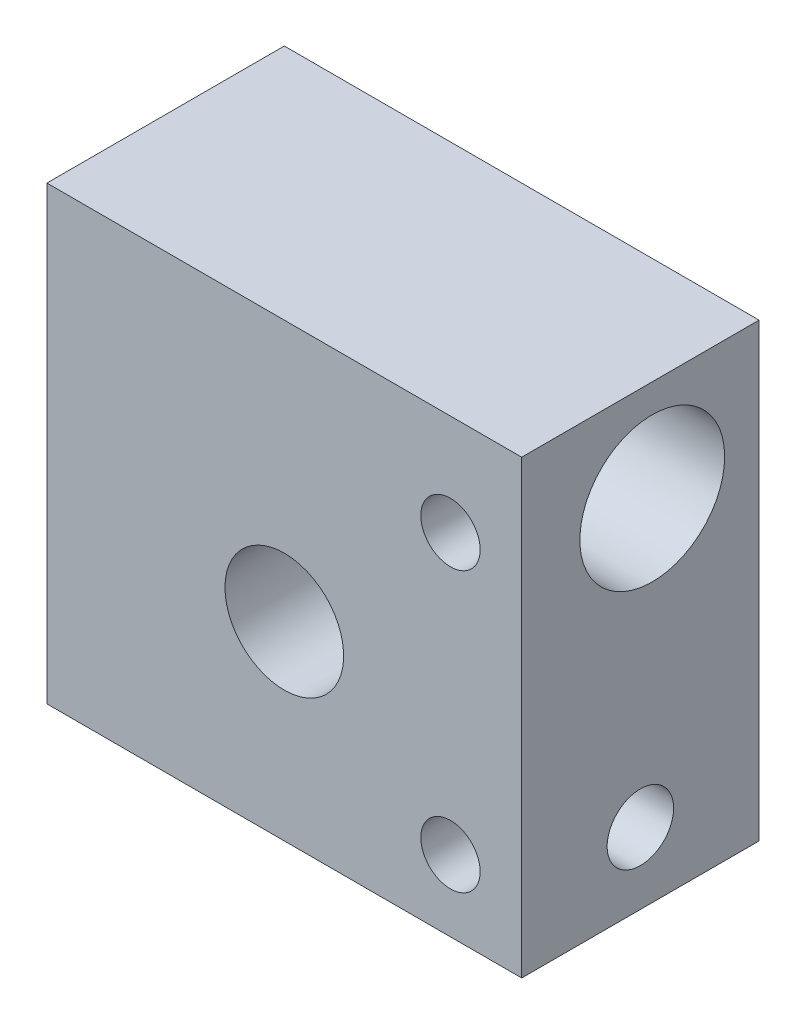
SolidWorks part; units mm, degrees
ref_plane "Front Plane" through (0, 0, 0) normal (0, 0, 1) x (1, 0, 0)
ref_plane "Top Plane" through (0, 0, 0) normal (0, 1, 0) x (1, 0, 0)
ref_plane "Right Plane" through (0, 0, 0) normal (1, 0, 0) x (0, 0, -1)
sketch "Sketch1" plane through (0, 0, 0) normal (0, 0, 1) x (1, 0, 0)
  line L1 (-10, -9.5) -> (10, -9.5)
  line L2 (-10, -9.5) -> (-10, 9.5)
  line L3 (-10, 9.5) -> (10, 9.5)
  line L4 (10, -9.5) -> (10, 9.5)
  line L5 (-10, -9.5) -> (10, 9.5) construction
  line L6 (-10, 9.5) -> (10, -9.5) construction
  point P0 (0, 0)
  dimension "D1" = 19
  dimension "D2" = 20
extrude "Boss-Extrude1" add sketch "Sketch1" along normal blind 10
sketch "Sketch2" plane through (0, 0, 0) normal (0, 0, -1) x (-1, 0, 0)
  line L0 (0, 9.5) -> (0, -9.5) construction
  line L1 (10, -9.5) -> (-10, -9.5) construction
  line L2 (-10, 9.5) -> (10, 9.5) construction
  circle A0 centre (0, -1.5) radius 2.5
  dimension "D1" = 5
  dimension "D2" = 8
extrude "Cut-Extrude1" cut sketch "Sketch2" against normal through all
cosmetic thread "Rosca cosmética1" parameters "D2"=6
sketch "Sketch3" plane through (10, 0, 0) normal (1, 0, 0) x (0, 0, -1)
  line L0 (-10, 0) -> (0, 0) construction
  line L1 (-10, -9.5) -> (-10, 9.5) construction
  line L2 (0, -9.5) -> (0, 9.5) construction
  line L3 (-4.5, 0) -> (-4.5, 9.5) construction
  line L5 (-10, 9.5) -> (0, 9.5) construction
  circle A0 centre (-4.5, 5.25) radius 3.05
  dimension "D1" = 6.1
  dimension "D3" = 4.5
  dimension "D2" = 1.2
extrude "Cut-Extrude2" cut sketch "Sketch3" against normal through all
sketch "Sketch4" plane through (10, 0, 0) normal (1, 0, 0) x (0, 0, -1)
  line L0 (0, -5) -> (-10, -5) construction
  line L3 (-5, -5) -> (-5, -9.5) construction
  line L4 (-10, -9.5) -> (0, -9.5) construction
  line L5 (0, -9.5) -> (0, 9.5) construction
  line L6 (-10, -9.5) -> (-10, 9.5) construction
  circle A0 centre (-5, -5) radius 1.4
  dimension "D1" = 2.8
  dimension "D2" = 4.5
extrude "Cut-Extrude3" [suppressed] cut sketch "Sketch4" against normal blind 4
hole_wizard "Diámetro de taladro Ø2.8 (2.8)1" positions "Croquis7" profile "Croquis6" hole size "Ø2.8" standard "Iso"
sketch "Croquis7" plane through (10, 0, 0) normal (1, 0, 0) x (0, 0, -1)
  line L0 (0, -6.5) -> (-10, -6.5) construction
  line L1 (0, -9.5) -> (0, 9.5) construction
  line L2 (-10, -9.5) -> (-10, 9.5) construction
  line L4 (-10, -9.5) -> (0, -9.5) construction
  point P0 (-5, -6.5)
  dimension "D1" = 3
sketch "Croquis6" plane through (10, -6.5, 5) normal (0, 1, 0) x (0, 0, -1)
  line L0 (0, 0) -> (0, 14.8412)
  line L1 (0, 14.8412) -> (1.4, 14)
  line L2 (1.4, 14) -> (1.4, 0)
  line L5 (1.4, 0) -> (0, 0)
  line L10 (0, 14.8412) -> (-1.4, 14) construction
  line L11 (0, -6.35) -> (0, 107.95) construction
  dimension "Diámetro de taladro" = 2.8
  dimension "Profundidad de taladro" = 14
  dimension "Ángulo de perforador" = 118
hole_wizard "Taladro roscado M31" positions "Croquis3" profile "Croquis2" tap size "M3" standard "Iso"
sketch "Croquis3" plane through (-2.6487, -2.9752, 10) normal (0, 0, -1) x (1, 0, 0)
  line L3 (12.6487, -8.2252) -> (-7.3513, -8.2252) construction
  line L4 (12.6487, 6.5248) -> (12.6487, -12.4752) construction
  line L5 (-7.3513, -12.4752) -> (-7.3513, 6.5248) construction
  line L7 (12.6487, -11.2752) -> (12.6487, -5.1752) construction
  line L8 (12.6487, 3.5248) -> (-7.3513, 3.5248) construction
  line L10 (12.6487, 2.1248) -> (12.6487, 4.9248) construction
  point P0 (9.6487, -8.2252)
  point P28 (9.6487, 3.5248)
  dimension "D1" = 3
  dimension "D2" = 3
sketch "Croquis2" plane through (7, 5.25, 10) normal (1, 0, 0) x (0, -1, 0)
  line L0 (0, 0) -> (0, 2.45)
  line L1 (0, 2.45) -> (1.25, 2.45)
  line L2 (1.25, 2.45) -> (1.25, 0)
  line L5 (1.25, 0) -> (0, 0)
  line L11 (0, -6.35) -> (0, 107.95) construction
  dimension "Diámetro de perforador para roscar hasta el siguiente" = 2.5
  dimension "Profundidad de perforador para roscar hasta el siguiente" = 2.45
cosmetic thread "Rosca de taladro1" parameters "D2"=3
cosmetic thread "Rosca de taladro4" parameters "D2"=3
sketch "Croquis4" [suppressed] plane through (0, 0, 0) normal (0, 0, -1) x (-1, 0, 0)
  line L2 (-9, -9) -> (-9, 9) construction
  line L3 (-9, -3.1) -> (-9, -5.9) construction
  line L4 (-9, -3.1) -> (-9, -5.9) construction
  line L5 (-9, -4.5) -> (-6.5, -4.5) construction
  line L6 (9, -9) -> (-9, -9) construction
  circle A0 centre (-6.5, -4.5) radius 1.5
  dimension "D1" = 1
  dimension "D2" = 3
extrude "Cortar-Extruir1" [suppressed] cut sketch "Croquis4" against normal blind 5
sketch "Croquis5" plane through (10, 0, 0) normal (1, 0, 0) x (0, 0, -1)
  line L0 (0, -9.5) -> (0, 9.5) construction
  line L1 (-10, -9.5) -> (0, -9.5) construction
  point P0 (-5, -5)
  dimension "D1" = 5
  dimension "D2" = 4.5
sketch "Croquis8" plane through (0, 0, 10) normal (0, 0, 1) x (1, 0, 0)
  line L1 (10, 5.25) -> (-10, 5.25) construction
  line L2 (10, -9.5) -> (10, 9.5) construction
  line L3 (-10, 9.5) -> (-10, -9.5) construction
  line L4 (10, 2.2) -> (10, 8.3) construction
  line L5 (-10, 8.3) -> (-10, 2.2) construction
  point P0 (0, 5.25)
hole_wizard "Taladro roscado M33" [suppressed] positions "Croquis10" profile "Croquis9" tap size "M3" standard "Iso"
sketch "Croquis10" plane through (0, 0, 10) normal (0, 0, 1) x (1, 0, 0)
  point P0 (0, 3.975)
sketch "Croquis9" plane through (0, 3.975, 10) normal (1, 0, 0) x (0, -1, 0)
  line L0 (0, 0) -> (0, 1.975)
  line L1 (0, 1.975) -> (1.25, 1.975)
  line L2 (1.25, 1.975) -> (1.25, 0)
  line L5 (1.25, 0) -> (0, 0)
  line L11 (0, -6.35) -> (0, 107.95) construction
  dimension "Diámetro de perforador para roscar hasta el siguiente" = 2.5
  dimension "Profundidad de perforador para roscar hasta el siguiente" = 1.975
cosmetic thread "Rosca de taladro3" [suppressed] parameters "D2"=3
